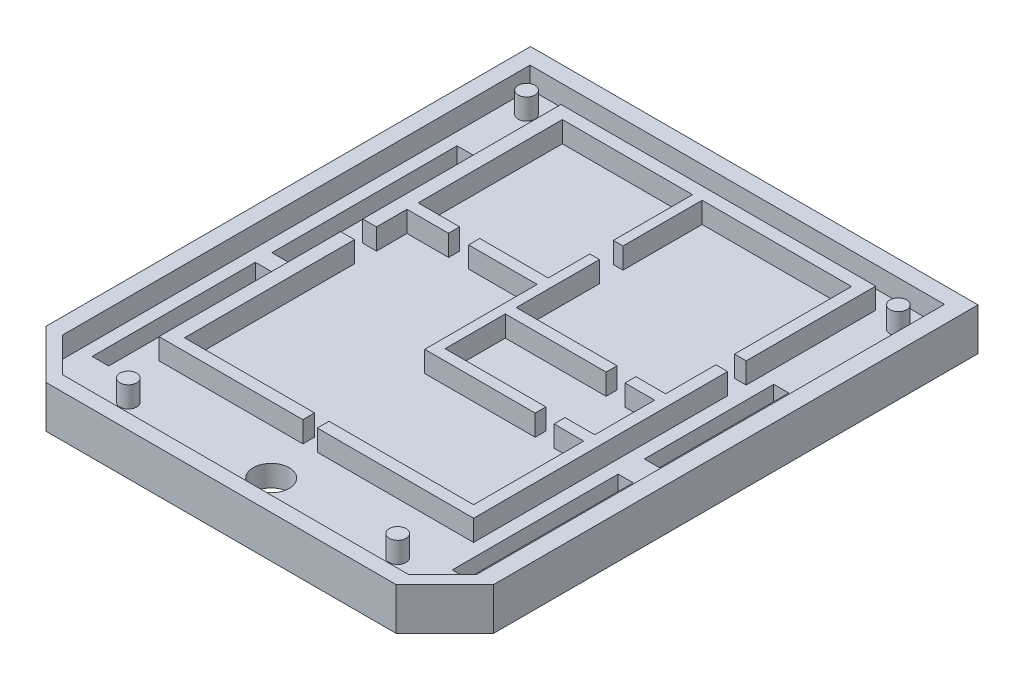
SolidWorks part; units mm, degrees
ref_plane "Front Plane" through (0, 0, 0) normal (0, 0, 1) x (1, 0, 0)
ref_plane "Top Plane" through (0, 0, 0) normal (0, 1, 0) x (1, 0, 0)
ref_plane "Right Plane" through (0, 0, 0) normal (1, 0, 0) x (0, 0, -1)
sketch "Sketch1" plane through (0, 0, 0) normal (0, 1, 0) x (1, 0, 0)
  line L0 (-24.7167, 29.6898) -> (-24.7167, 27.4905)
  line L1 (-24.7167, 6.5966) -> (-22.3996, 4.2795)
  line L2 (-22.3996, 4.2795) -> (-5.7081, 4.2795)
  line L3 (-5.7081, 4.2795) -> (-3.3909, 6.5966)
  line L4 (-3.3909, 6.5966) -> (-3.3909, 29.6898)
  line L5 (-3.3909, 29.6898) -> (-24.7167, 29.6898)
  line L6 (-24.7167, 27.4905) -> (-24.7167, 6.5966)
extrude "Boss-Extrude1" add sketch "Sketch1" along normal blind 2.0154
sketch "Sketch13" plane through (0, 2.0154, 0) normal (0, 1, 0) x (1, 0, 0)
  line L0 (-23.9624, 28.9111) -> (-23.9624, 6.6331)
  line L1 (-23.9624, 6.6331) -> (-22.3219, 4.9926)
  line L2 (-22.3219, 4.9926) -> (-5.8513, 4.9926)
  line L3 (-5.8513, 4.9926) -> (-4.2108, 6.6331)
  line L4 (-4.2108, 6.6331) -> (-4.2108, 28.9111)
  line L5 (-4.2108, 28.9111) -> (-23.9624, 28.9111)
extrude "Cut-Extrude4" cut sketch "Sketch13" against normal blind 1
sketch "Sketch14" plane through (0, 1.0154, 0) normal (0, 1, 0) x (1, 0, 0)
  line L1 (-23.3719, 24.8427) -> (-22.5844, 24.8427)
  line L2 (-23.3719, 24.8427) -> (-23.3719, 16.0168)
  line L3 (-23.3719, 16.0168) -> (-22.5844, 16.0168)
  line L4 (-22.5844, 24.8427) -> (-22.5844, 16.0168)
  line L5 (-23.3719, 15.2293) -> (-22.5844, 15.2293)
  line L6 (-23.3719, 15.2293) -> (-23.3719, 7.4533)
  line L7 (-23.3719, 7.4533) -> (-22.5844, 7.4533)
  line L8 (-22.5844, 15.2293) -> (-22.5844, 7.4533)
  line L9 (-5.9825, 22.546) -> (-5.2607, 22.546)
  line L10 (-5.9825, 22.546) -> (-5.9825, 16.3777)
  line L11 (-5.9825, 16.3777) -> (-5.2607, 16.3777)
  line L12 (-5.2607, 22.546) -> (-5.2607, 16.3777)
  line L13 (-5.9825, 15.1309) -> (-5.2607, 15.1309)
  line L14 (-5.9825, 15.1309) -> (-5.9825, 7.2237)
  line L15 (-5.9825, 7.2237) -> (-5.2607, 7.2237)
  line L16 (-5.2607, 15.1309) -> (-5.2607, 7.2237)
extrude "Cut-Extrude8" cut sketch "Sketch14" against normal blind 2
sketch "Sketch16" plane through (0, 1.0154, 0) normal (0, 1, 0) x (1, 0, 0)
  circle A0 centre (-14.0866, 6.6987) radius 0.8587
extrude "Cut-Extrude9" cut sketch "Sketch16" against normal blind 2
sketch "Sketch17" plane through (0, 1.0154, 0) normal (0, 1, 0) x (1, 0, 0)
  line L0 (-21.6001, 28.0252) -> (-6.6059, 28.0252)
  line L1 (-6.6059, 28.0252) -> (-6.6059, 21.8569)
  line L2 (-6.6059, 21.8569) -> (-7.1637, 21.8569)
  line L3 (-7.1637, 21.8569) -> (-7.1637, 27.4346)
  line L4 (-7.1637, 27.4346) -> (-20.9439, 27.4346)
  line L5 (-20.9439, 27.4346) -> (-20.9439, 18.5759)
  line L6 (-20.9439, 18.5759) -> (-21.6001, 18.5759)
  line L7 (-21.6001, 18.5759) -> (-21.6001, 28.0252)
  line L8 (-21.6001, 17.526) -> (-21.6001, 8.8642)
  line L9 (-21.6001, 8.8642) -> (-14.7428, 8.8642)
  line L10 (-14.7428, 8.8642) -> (-14.7428, 9.4219)
  line L11 (-14.7428, 9.4219) -> (-20.9439, 9.4219)
  line L12 (-20.9439, 9.4219) -> (-20.9439, 17.526)
  line L13 (-20.9439, 17.526) -> (-21.6001, 17.526)
  line L14 (-14.0538, 9.4219) -> (-14.0538, 8.8642)
  line L15 (-14.0538, 8.8642) -> (-6.6059, 8.8642)
  line L16 (-6.6059, 8.8642) -> (-6.6059, 20.9711)
  line L17 (-6.6059, 20.9711) -> (-7.1637, 20.9711)
  line L18 (-7.1637, 20.9711) -> (-7.1637, 9.4219)
  line L19 (-7.1637, 9.4219) -> (-14.0538, 9.4219)
  line L20 (-14.7428, 27.4346) -> (-14.7428, 23.6615)
  line L21 (-14.7428, 23.6615) -> (-14.2835, 23.6615)
  line L22 (-14.2835, 23.6615) -> (-14.2835, 27.4346)
  line L23 (-14.7428, 22.5423) -> (-14.2835, 22.5423)
  line L24 (-14.2835, 22.5423) -> (-14.2835, 18.5759)
  line L25 (-14.2835, 18.5759) -> (-9.4788, 18.5759)
  line L26 (-9.4788, 18.5759) -> (-9.4788, 18.0542)
  line L27 (-9.4788, 18.0542) -> (-14.7428, 18.0542)
  line L28 (-14.7428, 18.0542) -> (-14.7428, 22.5423)
  line L29 (-7.1637, 18.5759) -> (-8.5812, 18.5759)
  line L30 (-8.5812, 18.5759) -> (-8.5812, 18.0542)
  line L31 (-8.5812, 18.0542) -> (-7.1637, 18.0542)
  line L32 (-7.1637, 18.0542) -> (-7.1637, 18.5759)
  line L33 (-14.7428, 20.5591) -> (-18.0062, 20.5591)
  line L34 (-18.0062, 20.5591) -> (-18.0062, 20.0289)
  line L35 (-18.0062, 20.0289) -> (-14.7428, 20.0289)
  line L36 (-14.7428, 20.0289) -> (-14.7428, 20.5591)
  line L37 (-20.9439, 20.5591) -> (-18.9636, 20.5591)
  line L38 (-18.9636, 20.5591) -> (-18.9636, 20.0289)
  line L39 (-18.9636, 20.0289) -> (-20.9439, 20.0289)
  line L40 (-20.9439, 20.0289) -> (-20.9439, 20.5591)
  line L41 (-14.7428, 18.0542) -> (-14.7428, 14.6731)
  line L42 (-14.7428, 14.6731) -> (-9.4788, 14.6731)
  line L43 (-9.4788, 14.6731) -> (-9.4788, 15.1818)
  line L44 (-9.4788, 15.1818) -> (-14.2835, 15.1818)
  line L45 (-14.2835, 15.1818) -> (-14.2835, 18.0542)
  line L46 (-14.2835, 18.0542) -> (-14.7428, 18.0542)
  line L47 (-7.1637, 15.1965) -> (-8.5812, 15.1965)
  line L48 (-8.5812, 15.1965) -> (-8.5812, 14.6731)
  line L49 (-8.5812, 14.6731) -> (-7.1637, 14.6731)
  line L50 (-7.1637, 14.6731) -> (-7.1637, 15.1965)
extrude "Boss-Extrude5" add sketch "Sketch17" along normal blind 1 contours L7 L6 L5 L4 L3 L2 L1 L0 | L21 L22 L4 L20 | L34 L35 L28 L33 | L18 L19 L14 L15 L16 L17 | L30 L31 L18 L29 | L48 L49 L18 L47 | L37 L38 L39 L40 | L12 L13 L8 L9 L10 L11 | L41 L42 L43 L44 L45 L46
sketch "Sketch18" plane through (0, 1.0154, 0) normal (0, 1, 0) x (1, 0, 0)
  circle A0 centre (-23.0109, 27.7956) radius 0.4005
  circle A1 centre (-20.6226, 6.4262) radius 0.4005
  circle A2 centre (-5.2935, 27.7956) radius 0.4005
  circle A3 centre (-7.7871, 6.4262) radius 0.4005
extrude "Boss-Extrude6" add sketch "Sketch18" along normal blind 1
